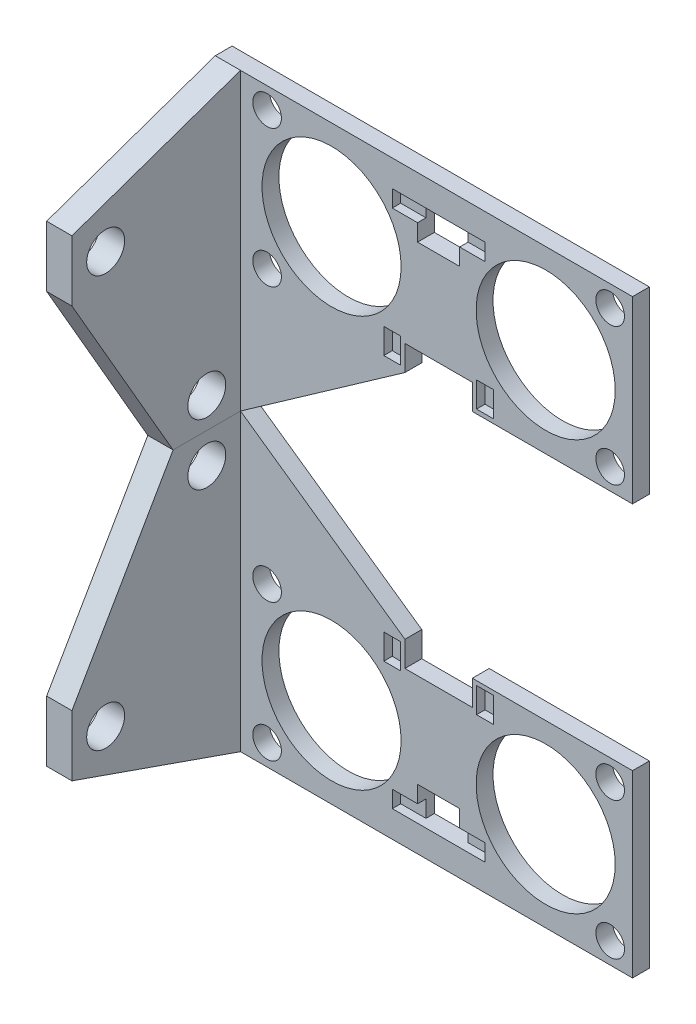
SolidWorks part; units mm, degrees
material "ABS"
ref_plane "前基準面" through (0, 0, 0) normal (0, 0, 1) x (1, 0, 0)
ref_plane "上基準面" through (0, 0, 0) normal (0, 1, 0) x (1, 0, 0)
ref_plane "右基準面" through (0, 0, 0) normal (1, 0, 0) x (0, 0, -1)
sketch "草圖1" plane through (0, 0, 0) normal (0, 0, 1) x (1, 0, 0)
  line L1 (-23, -10.65) -> (23, -10.65)
  line L2 (-23, -10.65) -> (-23, 10.65)
  line L3 (-23, 10.65) -> (23, 10.65)
  line L4 (23, -10.65) -> (23, 10.65)
  line L5 (-23, -10.65) -> (23, 10.65) construction
  line L6 (-23, 10.65) -> (23, -10.65) construction
  point P0 (0, 0)
  dimension "D1" = 46
  dimension "D2" = 21.3
extrude "填料-伸長1" add sketch "草圖1" along normal blind 2
sketch "草圖2" plane through (0, 0, 2) normal (0, 0, 1) x (1, 0, 0)
  line L0 (-12.7, 0) -> (12.7, 0) construction
  circle A0 centre (-12.7, 0) radius 8.25
  circle A1 centre (12.7, 0) radius 8.25
  point P4 (0, 0)
  dimension "D1" = 25.4
  dimension "D2" = 16.5
extrude "除料-伸長1" cut sketch "草圖2" against normal through all
sketch "草圖3" plane through (0, 0, 2) normal (0, 0, 1) x (1, 0, 0)
  line L0 (0, 0) -> (0, 9.15) construction
  line L1 (23, 10.65) -> (-23, 10.65) construction
  line L2 (-4, 7.65) -> (4, 7.65)
  line L3 (-4, 7.65) -> (-4, 10.65)
  line L4 (-4, 10.65) -> (4, 10.65)
  line L5 (4, 7.65) -> (4, 10.65)
  line L6 (-4, 7.65) -> (4, 10.65) construction
  line L7 (-4, 10.65) -> (4, 7.65) construction
  dimension "D1" = 8
  dimension "D2" = 3
extrude "除料-伸長2" cut sketch "草圖3" against normal through all
sketch "草圖4" plane through (0, 0, 2) normal (0, 0, 1) x (1, 0, 0)
  line L0 (0, 0) -> (0, -5.5) construction
  line L2 (-2.5, -3.5) -> (2.5, -3.5)
  line L3 (-2.5, -3.5) -> (-2.5, -7.5)
  line L4 (-2.5, -7.5) -> (2.5, -7.5)
  line L5 (2.5, -3.5) -> (2.5, -7.5)
  line L6 (-2.5, -3.5) -> (2.5, -7.5) construction
  line L7 (-2.5, -7.5) -> (2.5, -3.5) construction
  dimension "D1" = 5
  dimension "D2" = 4
  dimension "D3" = 5.5
extrude "除料-伸長3" cut sketch "草圖4" against normal through all
sketch "草圖5" plane through (0, 0, 2) normal (0, 0, 1) x (1, 0, 0)
  line L0 (0, 0) -> (0, 8.65) construction
  line L1 (2.5, -7.5) -> (5.5, -7.5)
  line L2 (2.5, -7.5) -> (2.5, -5.5)
  line L3 (2.5, -5.5) -> (5.5, -5.5)
  line L4 (5.5, -7.5) -> (5.5, -5.5)
  line L5 (-5.5, 8.65) -> (5.5, 8.65) construction
  line L6 (23, 10.65) -> (4, 10.65) construction
  line L7 (-4.5, 10.15) -> (-6.5, 10.15)
  line L8 (-4.5, 10.15) -> (-4.5, 7.15)
  line L9 (-4.5, 7.15) -> (-6.5, 7.15)
  line L10 (-6.5, 10.15) -> (-6.5, 7.15)
  line L11 (-4.5, 10.15) -> (-6.5, 7.15) construction
  line L12 (-4.5, 7.15) -> (-6.5, 10.15) construction
  line L13 (6.5, 10.15) -> (4.5, 10.15)
  line L14 (6.5, 10.15) -> (6.5, 7.15)
  line L15 (6.5, 7.15) -> (4.5, 7.15)
  line L16 (4.5, 10.15) -> (4.5, 7.15)
  line L17 (6.5, 10.15) -> (4.5, 7.15) construction
  line L18 (6.5, 7.15) -> (4.5, 10.15) construction
  line L20 (-2.5, -7.5) -> (-5.5, -7.5)
  line L21 (-2.5, -7.5) -> (-2.5, -5.5)
  line L22 (-2.5, -5.5) -> (-5.5, -5.5)
  line L23 (-5.5, -7.5) -> (-5.5, -5.5)
  point P10 (0, 8.65)
  dimension "D1" = 2
  dimension "D2" = 3
  dimension "D3" = 2
  dimension "D4" = 3
  dimension "D5" = 11
  dimension "D6" = 0.5
extrude "除料-伸長4" cut sketch "草圖5" against normal blind 1
hole_wizard "M3 餘隙孔1" positions "草圖6" profile "草圖7" hole size "M3" standard "Ansi Metric" end condition through all
sketch "草圖6" plane through (0, 0, 2) normal (0, 0, 1) x (1, 0, 0)
  line L1 (-20.35, -8.15) -> (20.35, -8.15) construction
  line L2 (-20.35, -8.15) -> (-20.35, 8.15) construction
  line L3 (-20.35, 8.15) -> (20.35, 8.15) construction
  line L4 (20.35, -8.15) -> (20.35, 8.15) construction
  line L5 (-20.35, -8.15) -> (20.35, 8.15) construction
  line L6 (-20.35, 8.15) -> (20.35, -8.15) construction
  point P1 (20.35, 8.15)
  point P112 (-20.35, -8.15)
  point P113 (-20.35, 8.15)
  point P114 (20.35, -8.15)
  dimension "D1" = 16.3
  dimension "D2" = 40.7
sketch "草圖7" plane through (20.35, 8.15, 2) normal (1, 0, 0) x (0, -1, 0)
  line L0 (0, 0) -> (0, 2)
  line L1 (0, 2) -> (1.7, 2)
  line L2 (1.7, 2) -> (1.7, 0)
  line L5 (1.7, 0) -> (0, 0)
  line L11 (0, -6.35) -> (0, 107.95) construction
  dimension "貫穿孔直徑" = 3.4
  dimension "貫穿孔深度" = 2
sketch "草圖11" plane through (-23, 0, 0) normal (-1, 0, 0) x (0, 0, 1)
  line L1 (2, 10.65) -> (0, 10.65)
  line L2 (2, 10.65) -> (2, -10.65)
  line L3 (2, -10.65) -> (0, -10.65)
  line L4 (0, 10.65) -> (0, -10.65)
extrude "填料-伸長4" add sketch "草圖11" along normal blind 0.5
sketch "草圖12" plane through (0, 0, 0) normal (0, 0, 1) x (1, 0, 0)
  line L1 (-23.5, -10.65) -> (-26.5, -10.65)
  line L2 (-23.5, -10.65) -> (-23.5, 24.35)
  line L3 (-23.5, 24.35) -> (-26.5, 24.35)
  line L4 (-26.5, -10.65) -> (-26.5, 24.35)
  dimension "D1" = 3
  dimension "D2" = 35
extrude "填料-伸長5" add sketch "草圖12" along normal up to surface (2 mm away) up to face at (22.05, 8.15, 2)
sketch "草圖17" plane through (0, 0, 2) normal (0, 0, 1) x (1, 0, 0)
  line L0 (-26.5, -10.65) -> (-26.5, 24.35) construction
  line L1 (-23.5, 24.35) -> (-26.5, 24.35)
  line L2 (-23.5, 24.35) -> (-23.5, -3.65)
  line L3 (-23.5, -3.65) -> (-26.5, -3.65)
  line L4 (-26.5, 24.35) -> (-26.5, -3.65)
  dimension "D1" = 28
extrude "填料-伸長8" add sketch "草圖17" along normal blind 20
hole_wizard "M4 餘隙孔2" positions "草圖20" profile "草圖21" hole size "M4" standard "Ansi Metric" end condition through all
sketch "草圖20" plane through (-26.5, 0, 0) normal (-1, 0, 0) x (0, 0, 1)
  line L0 (6, 20.7423) -> (18, -0.0423) construction
  line L1 (0, 24.35) -> (0, -10.65) construction
  line L2 (22, 10.35) -> (12, 10.35) construction
  line L3 (22, 24.35) -> (22, -3.65) construction
  point P1 (6, 20.7423)
  point P2 (18, -0.0423)
  dimension "D1" = 24
  dimension "D2" = 30
  dimension "D3" = 4
sketch "草圖21" plane through (-26.5, 20.7423, 6) normal (0, 1, 0) x (0, 0, 1)
  line L0 (0, 0) -> (0, 49.5)
  line L1 (0, 49.5) -> (2.25, 49.5)
  line L2 (2.25, 49.5) -> (2.25, 0)
  line L5 (2.25, 0) -> (0, 0)
  line L11 (0, -6.35) -> (0, 107.95) construction
  dimension "貫穿孔直徑" = 4.5
  dimension "貫穿孔深度" = 49.5
sketch "草圖22" plane through (-26.5, 0, 0) normal (-1, 0, 0) x (0, 0, 1)
  line L0 (22, -3.65) -> (2, -10.65)
  line L1 (2, -10.65) -> (2, -3.65)
  line L2 (2, -3.65) -> (22, -3.65)
extrude "填料-伸長9" add sketch "草圖22" against normal up to surface (3 mm away) up to face at (-23.5, 20.7423, 8.25)
chamfer "導角1" distance 12 angle 60 1 edges at (-25, 24.35, 22)
sketch "草圖23" plane through (0, 0, 0) normal (0, 0, -1) x (-1, 0, 0)
  line L0 (4, 10.65) -> (23.5, 24.35)
  line L1 (23.5, 24.35) -> (23.5, 10.65)
  line L2 (23.5, 10.65) -> (4, 10.65)
extrude "填料-伸長10" add sketch "草圖23" against normal up to surface (2 mm away) up to face at (22.05, 8.15, 2)
ref_plane "平面1" through (0, 24.35, 0) normal (0, 1, 0) x (1, 0, 0)
mirror "鏡射1" about plane through (0, 24.35, 0) normal (0, 1, 0) of bodies 130 117
split "分割1" trim tools "平面1" bodies to split 130 119 resulting bodies 120 121
